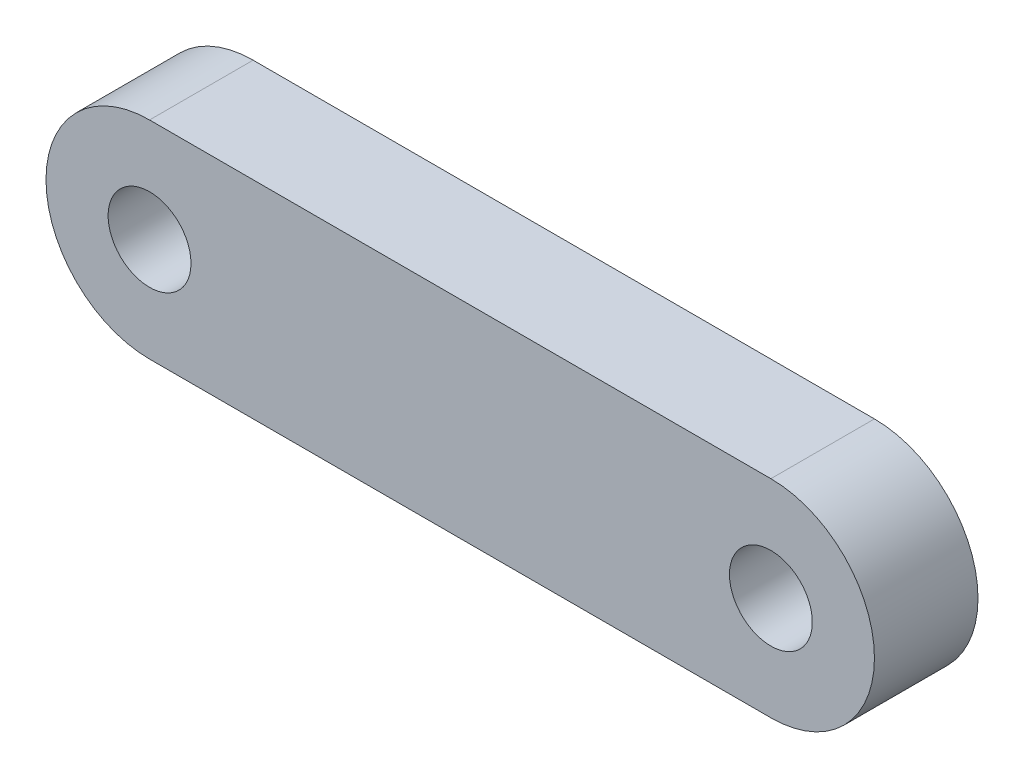
SolidWorks part; units mm, degrees
material "Thornel Mat VMA"
ref_plane "前视基准面" through (0, 0, 0) normal (0, 0, 1) x (1, 0, 0)
ref_plane "上视基准面" through (0, 0, 0) normal (0, 1, 0) x (1, 0, 0)
ref_plane "右视基准面" through (0, 0, 0) normal (1, 0, 0) x (0, 0, -1)
sketch "草图1" plane through (0, 0, 0) normal (0, 0, 1) x (1, 0, 0)
  line L0 (-15, 5) -> (15, 5)
  line L1 (-15, -5) -> (15, -5)
  line L2 (0, -55) -> (0, 55) construction
  circle A0 centre (-15, 0) radius 2
  arc A1 (-15, 5) -> (-15, -5) centre (-15, 0) ccw
  arc A2 (15, 5) -> (15, -5) centre (15, 0) cw
  circle A3 centre (15, 0) radius 2
  dimension "D2" = 4
  dimension "D3" = 10
  dimension "D4" = 5
  dimension "D1" = 15
extrude "凸台-拉伸1" add sketch "草图1" along normal blind 5
